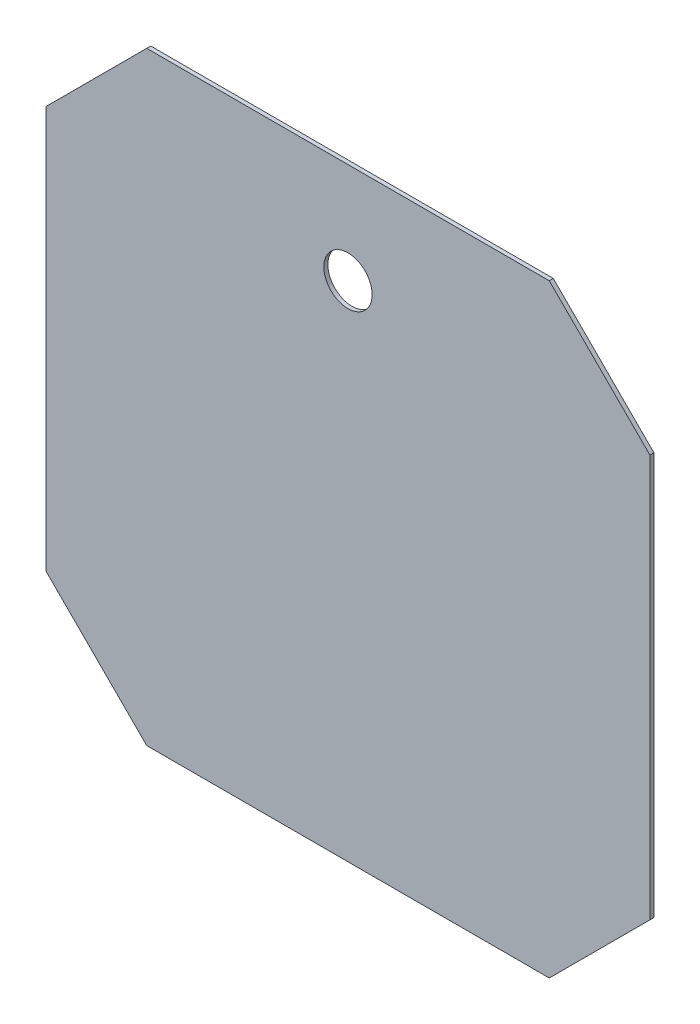
SolidWorks part; units mm, degrees
ref_plane "Front Plane" through (0, 0, 0) normal (0, 0, 1) x (1, 0, 0)
ref_plane "Top Plane" through (0, 0, 0) normal (0, 1, 0) x (1, 0, 0)
ref_plane "Right Plane" through (0, 0, 0) normal (1, 0, 0) x (0, 0, -1)
sketch "Sketch1" plane through (0, 0, 0) normal (0, 0, 1) x (1, 0, 0)
  line L0 (-75, 50) -> (-50, 75)
  line L1 (-50, 75) -> (50, 75)
  line L2 (-75, 50) -> (-75, -50)
  line L3 (-50, -75) -> (50, -75)
  line L4 (75, 50) -> (75, -50)
  line L5 (0, 75) -> (0, -75) construction
  line L6 (-75, 0) -> (75, 0) construction
  line L7 (75, 50) -> (50, 75)
  line L8 (75, -50) -> (50, -75)
  line L9 (-75, -50) -> (-50, -75)
  circle A0 centre (0, 50) radius 6
  dimension "D1" = 12
  dimension "D2" = 150
  dimension "D3" = 135
  dimension "D4" = 150
  dimension "D5" = 25
extrude "Boss-Extrude1" add sketch "Sketch1" along normal blind 1
